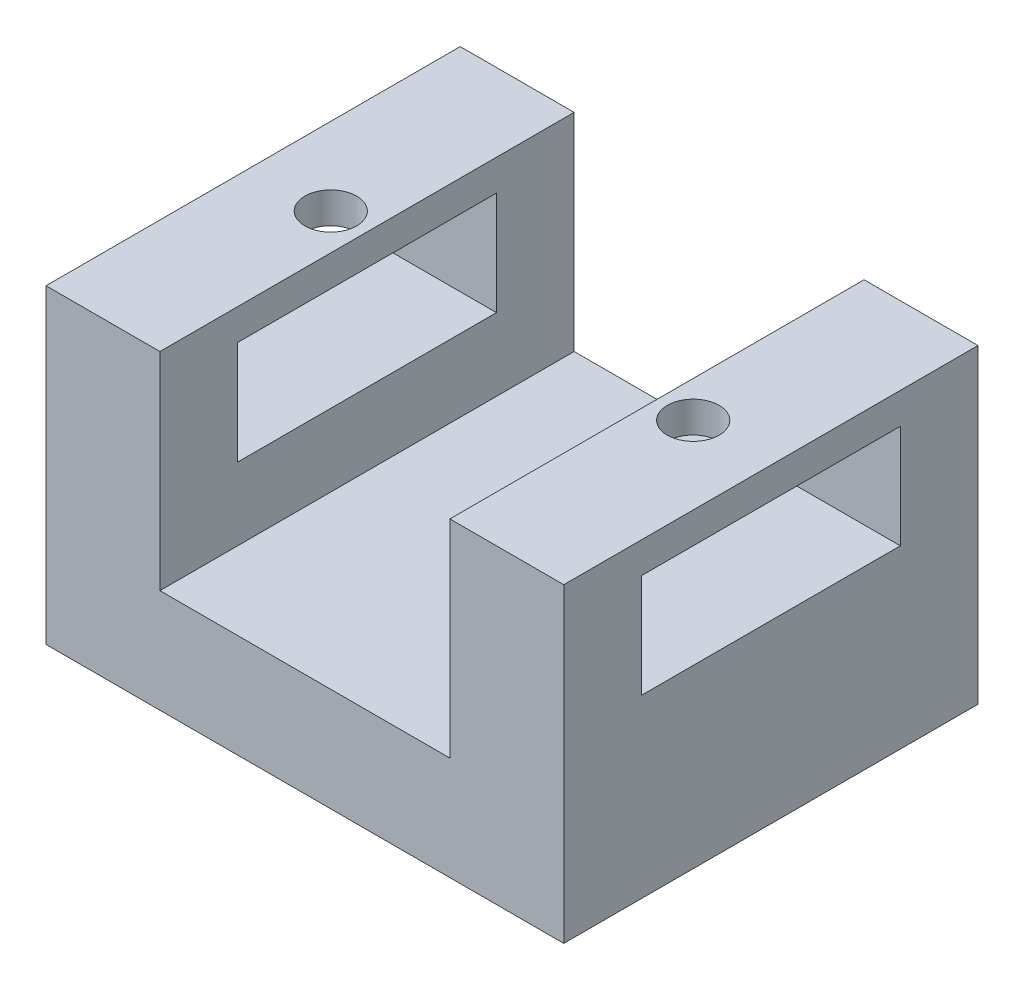
SolidWorks part; units mm, degrees
ref_plane "Front Plane" through (0, 0, 0) normal (0, 0, 1) x (1, 0, 0)
ref_plane "Top Plane" through (0, 0, 0) normal (0, 1, 0) x (1, 0, 0)
ref_plane "Right Plane" through (0, 0, 0) normal (1, 0, 0) x (0, 0, -1)
sketch "Sketch1" plane through (0, 0, 0) normal (0, 1, 0) x (1, 0, 0)
  line L1 (0, 0) -> (50, 0)
  line L2 (0, 0) -> (0, 40)
  line L3 (0, 40) -> (50, 40)
  line L4 (50, 0) -> (50, 40)
  dimension "D1" = 50
  dimension "D2" = 40
extrude "Boss-Extrude1" add sketch "Sketch1" along normal blind 10
ref_plane "Plane1" through (25, 0, 0) normal (-1, 0, 0) x (0, 0, 1)
ref_plane "Plane2" through (0, 0, -20) normal (0, 0, -1) x (-1, 0, 0)
sketch "Sketch3" plane through (0, 10, 0) normal (0, 1, 0) x (1, 0, 0)
  line L0 (0, 0) -> (50, 0) construction
  line L1 (0, 40) -> (11, 40)
  line L2 (0, 40) -> (0, 0)
  line L3 (0, 0) -> (11, 0)
  line L4 (11, 40) -> (11, 0)
  line L5 (25, 5.5) -> (25, -5.5) construction
  dimension "D1" = 14
extrude "Boss-Extrude2" add sketch "Sketch3" along normal blind 20
mirror "Mirror1" about plane through (25, 0, 0) normal (-1, 0, 0) of "Boss-Extrude2"
sketch "Sketch4" plane through (50, 0, 0) normal (1, 0, 0) x (0, 0, -1)
  line L0 (20, -5.5) -> (20, 5.5) construction
  line L1 (7.5, 27) -> (32.5, 27)
  line L2 (7.5, 27) -> (7.5, 17)
  line L3 (7.5, 17) -> (32.5, 17)
  line L4 (32.5, 27) -> (32.5, 17)
  line L5 (40, 30) -> (0, 30) construction
  point P4 (20, 27)
  dimension "D1" = 10
  dimension "D2" = 3
  dimension "D3" = 25
extrude "Cut-Extrude1" cut sketch "Sketch4" against normal through all
sketch "Sketch5" plane through (0, 30, 0) normal (0, 1, 0) x (1, 0, 0)
  line L0 (5.5, 20) -> (-5.5, 20) construction
  line L3 (25, 5.5) -> (25, -5.5) construction
  circle A0 centre (7.5, 20) radius 2.5
  dimension "D1" = 5
  dimension "D2" = 17.5
extrude "Cut-Extrude2" cut sketch "Sketch5" against normal up to surface (13 mm away) up to face at (5.5, 17, -20)
mirror "Mirror2" about plane through (25, 0, 0) normal (-1, 0, 0) of "Cut-Extrude2"
